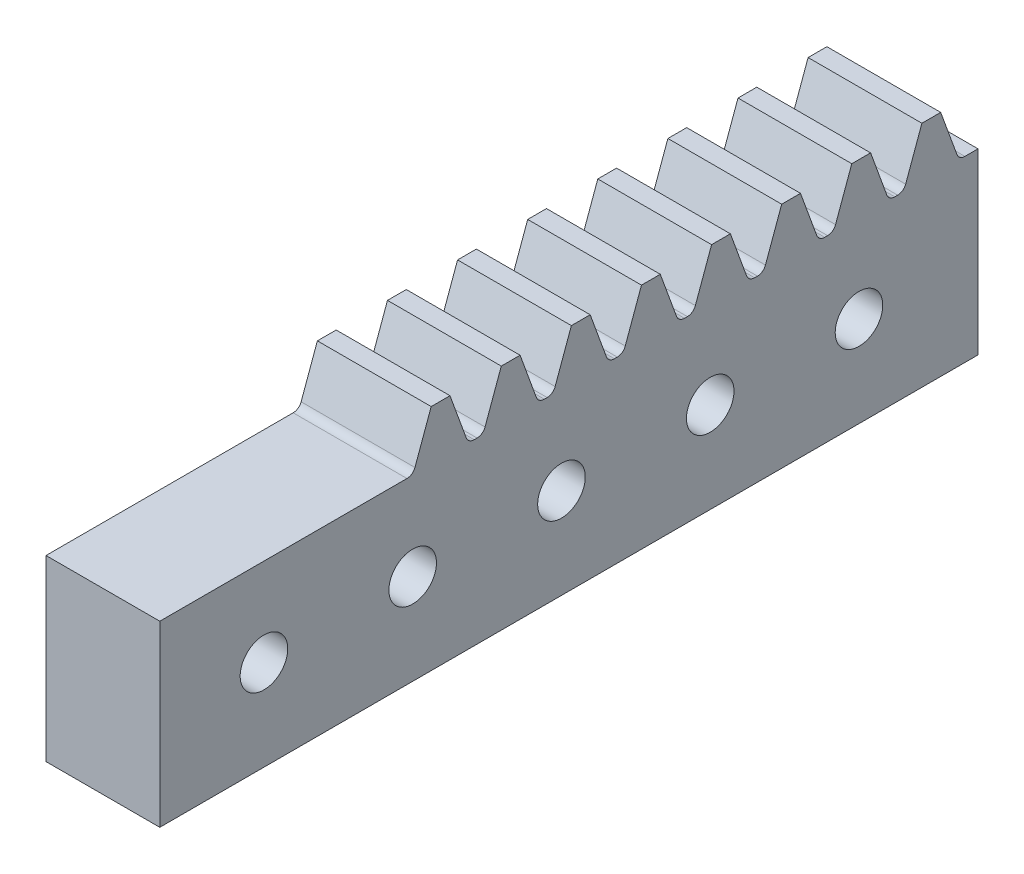
SolidWorks part; units mm, degrees
ref_plane "Front Plane" through (0, 0, 0) normal (0, 0, 1) x (1, 0, 0)
ref_plane "Top Plane" through (0, 0, 0) normal (0, 1, 0) x (1, 0, 0)
ref_plane "Right Plane" through (0, 0, 0) normal (1, 0, 0) x (0, 0, -1)
sketch "Esquisse1" plane through (0, 0, 0) normal (0, 0, 1) x (1, 0, 0)
  line L1 (-12, 15) -> (12, 15)
  line L2 (-12, 15) -> (-12, -15)
  line L3 (-12, -15) -> (12, -15)
  line L4 (12, 15) -> (12, -15)
  point P4 (0, -15)
  point P5 (-12, 0)
  dimension "D1" = 24
  dimension "D2" = 30
extrude "Main Extrusion" add sketch "Esquisse1" along normal blind 30
sketch "Esquisse3" plane through (0, 0, 0) normal (0, 0, -1) x (-1, 0, 0)
  line L0 (-5.2, -1.6) -> (-5.2, -5.4)
  line L1 (-5.2, -5.4) -> (-4.2, -5.4)
  line L2 (-4.2, -5.4) -> (-4.2, -8.2)
  line L3 (-4.2, -8.2) -> (-5.2, -8.2)
  line L4 (-5.2, -8.2) -> (-5.2, -12)
  line L5 (-5.2, -12) -> (-1.4, -12)
  line L6 (-1.4, -12) -> (-1.4, -11)
  line L7 (-1.4, -11) -> (1.4, -11)
  line L8 (1.4, -11) -> (1.4, -12)
  line L9 (1.4, -12) -> (5.2, -12)
  line L10 (5.2, -12) -> (5.2, -8.2)
  line L11 (5.2, -8.2) -> (4.2, -8.2)
  line L12 (4.2, -8.2) -> (4.2, -5.4)
  line L13 (4.2, -5.4) -> (5.2, -5.4)
  line L14 (5.2, -5.4) -> (5.2, -1.6)
  line L15 (5.2, -1.6) -> (1.4, -1.6)
  line L16 (1.4, -1.6) -> (1.4, -2.6)
  line L17 (1.4, -2.6) -> (-1.4, -2.6)
  line L18 (-1.4, -2.6) -> (-1.4, -1.6)
  line L19 (-1.4, -1.6) -> (-5.2, -1.6)
  line L21 (12, -15) -> (-12, -15) construction
  point P20 (0, -11)
  point P24 (0, -15)
  dimension "D1" = 2.8
  dimension "D2" = 10.4
  dimension "D3" = 1
  dimension "D4" = 1
  dimension "D5" = 3
extrude "Main Riding Hole" cut sketch "Esquisse3" against normal through all
sketch "Esquisse4" plane through (-12, 0, 0) normal (-1, 0, 0) x (0, 0, 1)
  line L1 (0, -8.2) -> (0, -5.4) construction
  line L2 (0, 15) -> (0, -15) construction
  circle A0 centre (5, -6.8) radius 2.25
  point P5 (0, -6.8)
  dimension "D1" = 4.5
  dimension "D2" = 5
extrude "TractorHole" cut sketch "Esquisse4" against normal blind 8
mirror "TractorHoleSymetry" about plane through (0, 0, 0) normal (1, 0, 0) of "TractorHole"
sketch "Esquisse5" plane through (0, 0, 0) normal (1, 0, 0) x (0, 0, -1)
  line L0 (-45, 5) -> (-45, 35)
  line L2 (-45, 35) -> (-25, 35)
  line L3 (-25, 35) -> (-21.4735, 15)
  line L4 (-45, 5) -> (0, 5)
  line L5 (-21.4735, 15) -> (35, 15)
  line L6 (-30, -15) -> (-30, 15) construction
  line L7 (35, 15) -> (35, 3)
  line L8 (-30, -15) -> (0, -15) construction
  line L9 (0, 5) -> (0, 3)
  line L10 (0, -15) -> (0, 15) construction
  line L11 (0, 3) -> (35, 3)
  line L12 (-30, -15) -> (0, -15) construction
  dimension "D1" = 30
  dimension "D2" = 20
  dimension "D3" = 18
  dimension "D4" = 15
  dimension "D5" = 12
  dimension "D6" = 100
  dimension "D7" = 35
  dimension "D8" = 20
extrude "ImpactPiece" add sketch "Esquisse5" against normal mid plane 9
fillet "Congé1" radius 3 2 edges at (-4.5, 15, 25.7367) (4.5, 15, 25.7367)
sketch "Esquisse8" plane through (0, 0, 0) normal (1, 0, 0) x (0, 0, -1)
  line L0 (30, 15) -> (31.2284, 18.375)
  line L1 (31.2284, 18.375) -> (32.4927, 18.375)
  line L2 (32.4927, 18.375) -> (33.7211, 15)
  line L3 (30, 15) -> (29.0087, 15) construction
  line L4 (30, 15) -> (33.7211, 15)
  line L5 (30.1365, 15.375) -> (28.8722, 15.375) construction
  line L6 (30, 15) -> (30, 1.1813) construction
  line L7 (29.0087, 15) -> (28.3262, 16.875) construction
  line L8 (28.3262, 16.875) -> (33.0386, 16.875) construction
  line L9 (35, 15) -> (0, 15) construction
  line L10 (35, 3) -> (35, 15) construction
  dimension "D1" = 20
  dimension "D2" = 1.5
  dimension "D3" = 3.375
  dimension "D4" = 4.7124
  dimension "D5" = 3
  dimension "D6" = 5
extrude "Teeth" add sketch "Esquisse8" along normal mid plane 9
fillet "Congé3" radius 0.57 2 edges at (0, 15, -30) (0, 15, -33.7211)
pattern_linear "TeethRepetition" count 8 spacing 4.7124 along (0, 0, 1) of "Teeth", "Congé3"
sketch "Esquisse9" plane through (4.5, 0, 0) normal (1, 0, 0) x (0, 0, -1)
  line L0 (0, -15) -> (0, 15) construction
  line L1 (-20, 18.375) -> (35, 18.375)
  line L2 (-20, 18.375) -> (-20, 3)
  line L3 (-20, 3) -> (35, 3)
  line L4 (35, 18.375) -> (35, 3)
  line L5 (35, 3) -> (35, 15) construction
  line L8 (32.4927, 18.375) -> (31.2284, 18.375) construction
  dimension "D3" = 20
extrude "Bracket" cut sketch "Esquisse9" along normal mid plane 1.35
sketch "Esquisse10" plane through (4.5, 0, 0) normal (-1, 0, 0) x (0, 0, 1)
  line L4 (0, 3) -> (-35, 3) construction
  line L5 (-35, 3) -> (-35, 15) construction
  circle A0 centre (-27, 9.1) radius 1.6
  dimension "D1" = 3.2
  dimension "D2" = 6.1
  dimension "D3" = 8
extrude "BracketHole" cut sketch "Esquisse10" against normal through all both and the other way through all
pattern_linear "BracketHoleRepetition" count 5 spacing 10 along (0, 0, 1) of "BracketHole"
mirror "Symétrie1" about plane through (0, 0, 0) normal (1, 0, 0) of "Bracket"
sketch "Esquisse11" plane through (0, 0, 0) normal (0, 0, -1) x (-1, 0, 0)
  line L0 (12, 15) -> (12, -15) construction
  line L1 (12, 0.4) -> (4.5, 0.4)
  line L2 (12, 0.4) -> (12, 5.9)
  line L3 (12, 5.9) -> (4.5, 5.9)
  line L4 (4.5, 0.4) -> (4.5, 5.9)
  line L5 (4.5, 18) -> (4.5, 3) construction
  line L6 (5.2, -1.6) -> (1.4, -1.6) construction
  line L7 (4.5, 35) -> (4.5, 5) construction
  line L8 (4.5, 20) -> (12, 20)
  line L9 (4.5, 20) -> (4.5, 12.4)
  line L10 (4.5, 12.4) -> (12, 12.4)
  line L11 (12, 20) -> (12, 12.4)
  line L12 (12, 15) -> (12, -15) construction
  dimension "D1" = 2
  dimension "D2" = 5.5
  dimension "D3" = 6.5
extrude "RailHole" cut sketch "Esquisse11" against normal blind 20
sketch "Esquisse12" plane through (4.5, 0, 0) normal (1, 0, 0) x (0, 0, -1)
  line L0 (-45, 30) -> (-40, 35)
  line L1 (-45, 35) -> (-45, 5) construction
  line L2 (-25, 35) -> (-45, 35) construction
  line L3 (-40, 35) -> (-45, 35)
  line L4 (-45, 35) -> (-45, 30)
  dimension "D1" = 5
extrude "TopImpactCut" cut sketch "Esquisse12" against normal through all
mirror "Symétrie2" about plane through (12, 15, 30) normal (-1, 0, 0) of bodies 117
sketch "Esquisse13" plane through (0, 0, -35) normal (0, 0, -1) x (-1, 0, 0)
  line L0 (4.5, 35) -> (-4.5, 35) construction
  line L1 (-12, -15) -> (12, -15)
  line L2 (-12, -15) -> (-12, 35)
  line L3 (-12, 35) -> (12, 35)
  line L4 (12, -15) -> (12, 35)
extrude "MakerBeamMainHole" cut sketch "Esquisse13" against normal through all
sketch "Sketch1" plane through (0, 35, 0) normal (0, 1, 0) x (1, 0, 0)
  line L0 (12, 0) -> (12, -45)
  line L1 (12, -45) -> (36, -45)
  line L2 (36, -45) -> (36, 0)
  line L3 (36, 0) -> (27.825, 0.0519)
  line L4 (27.825, -0.494) -> (27.825, 0.5979) construction
  line L5 (27.825, 0.0519) -> (27.825, -20)
  line L6 (27.825, -20) -> (20.175, -20)
  line L7 (20.175, -20) -> (20.175, 0)
  line L8 (28.5, -45) -> (19.5, -45) construction
  line L9 (20.175, 0) -> (12, 0)
extrude "KeepOnlyTractor1" cut sketch "Sketch1" against normal through all
sketch "Sketch2" plane through (20.175, 0, 0) normal (-1, 0, 0) x (0, 0, 1)
  line L1 (0, 3) -> (20, 3)
  line L2 (0, 3) -> (0, -2.6)
  line L3 (0, -2.6) -> (20, -2.6)
  line L4 (20, 3) -> (20, -2.6)
extrude "KeepOnlyTractor2" cut sketch "Sketch2" against normal through all
